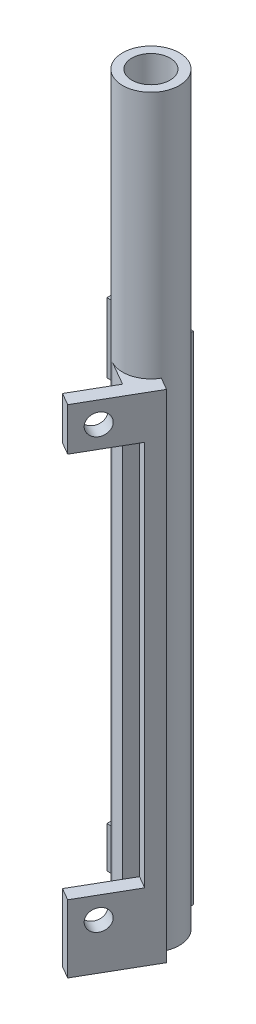
SolidWorks part; units mm, degrees
ref_plane "Front Plane" through (0, 0, 0) normal (0, 0, 1) x (1, 0, 0)
ref_plane "Top Plane" through (0, 0, 0) normal (0, 1, 0) x (1, 0, 0)
ref_plane "Right Plane" through (0, 0, 0) normal (1, 0, 0) x (0, 0, -1)
sketch "Sketch1" plane through (0, 0, 0) normal (0, 1, 0) x (1, 0, 0)
  circle A0 centre (0, 0) radius 5.08
  dimension "D1" = 10.16
extrude "Boss-Extrude1" add sketch "Sketch1" along normal blind 133.35
sketch "Sketch2" plane through (0, 0, 0) normal (0, -1, 0) x (1, 0, 0)
  circle A0 centre (0, 0) radius 3.429
  dimension "D1" = 6.858
extrude "Cut-Extrude1" cut sketch "Sketch2" against normal through all
sketch "Sketch3" plane through (0, 0, 0) normal (0, -1, 0) x (1, 0, 0)
  line L0 (0, 0) -> (0, -5.08) construction
  line L1 (0, -5.08) -> (-5.08, -5.08) construction
  line L2 (0, 0) -> (-2.54, 4.3994) construction
  line L3 (0, 0) -> (-5.08, 0) construction
  line L4 (-2.54, 4.3994) -> (1.8594, 6.9394) construction
  line L5 (8.7988, -5.08) -> (-1.4426, 12.6586) construction
  line L7 (0, -5.08) -> (-11.684, -5.08) construction
  line L8 (-1.4426, 12.6586) -> (-5.842, 10.1186)
  line L9 (-11.684, -5.08) -> (-11.684, 0)
  line L10 (-5.842, 10.1186) -> (-2.54, 4.3994)
  line L11 (-11.684, 0) -> (-5.08, 0)
  line L13 (-11.684, -5.08) -> (-11.684, -10.16)
  line L14 (-11.684, -10.16) -> (0, -10.16)
  line L15 (0, -10.16) -> (0, -5.08)
  line L17 (4.3994, 2.54) -> (8.7988, 5.08)
  line L18 (8.7988, 5.08) -> (2.9568, 15.1986)
  line L19 (2.9568, 15.1986) -> (-1.4426, 12.6586)
  arc A0 (-5.08, 0) -> (-2.54, 4.3994) centre (-0.7771, 0.4486) ccw
  circle A1 centre (0, 0) radius 3.429 construction
  circle A2 centre (0, 0) radius 5.08 construction
  arc A3 (4.3994, 2.54) -> (0, -5.08) centre (0, 0) cw
  point P9 (0, -5.08)
  dimension "D1" = 60
  dimension "D2" = 6.604
  dimension "D3" = 6.604
  dimension "D4" = 5.08
  dimension "D5" = 5.08
  dimension "D6" = 5.08
  dimension "D7" = 5.08
extrude "Boss-Extrude2" add sketch "Sketch3" against normal blind 88.9
sketch "Sketch4" plane through (0, 0, 0) normal (0, 0, 1) x (1, 0, 0)
  line L1 (-5.08, 88.9) -> (-5.08, 0) construction
  line L2 (-5.08, 88.9) -> (-11.684, 88.9) construction
  line L4 (-5.08, 0) -> (-11.684, 0) construction
  circle A0 centre (-8.89, 80.01) radius 1.905
  circle A1 centre (-8.89, 3.81) radius 1.905
  dimension "D3" = 3.81
  dimension "D5" = 3.81
  dimension "D2" = 76.2
  dimension "D1" = 8.89
  dimension "D4" = 3.81
extrude "Hole Cuts 1" cut sketch "Sketch4" against normal up to next
sketch "Sketch7" plane through (0, 0, 0) normal (0.866, 0, 0.5) x (0.5, 0, -0.866)
  line L0 (0, 0) -> (-11.684, 0) construction
  line L1 (-5.08, 88.9) -> (-5.08, 0) construction
  line L3 (-2.54, 88.9) -> (-5.842, 88.9) construction
  circle A0 centre (-8.89, 85.09) radius 1.905
  circle A1 centre (-8.89, 8.255) radius 1.905
  dimension "D2" = 3.81
  dimension "D5" = 8.255
  dimension "D1" = 3.81
  dimension "D3" = 3.81
  dimension "D4" = 76.835
extrude "Hole Cuts 2" cut sketch "Sketch7" along normal up to next
sketch "Sketch8" plane through (0, 0, 0) normal (0, -1, 0) x (1, 0, 0)
  line L0 (-5.842, 10.1186) -> (-1.8825, 12.4046)
  line L1 (2.9568, 15.1986) -> (-5.842, 10.1186) construction
  line L2 (-11.684, 0) -> (-11.684, -4.572)
  line L3 (-11.684, 0) -> (-11.684, -10.16) construction
  line L4 (-5.842, 10.1186) -> (-2.54, 4.3994)
  line L5 (-11.684, 0) -> (-5.08, 0)
  line L6 (-1.8825, 12.4046) -> (1.4195, 6.6854)
  line L7 (1.4195, 6.6854) -> (-2.54, 4.3994)
  line L8 (-11.684, -4.572) -> (-5.08, -4.572)
  line L9 (-5.08, -4.572) -> (-5.08, 0)
  dimension "D1" = 4.572
extrude "Cut-Extrude7" cut sketch "Sketch8" against normal up to next
sketch "Sketch9" plane through (0, 0, -10.16) normal (0, 0, -1) x (-1, 0, 0)
  line L1 (11.684, 88.9) -> (0, 88.9)
  line L2 (11.684, 88.9) -> (11.684, 0)
  line L3 (11.684, 0) -> (0, 0)
  line L4 (0, 88.9) -> (0, 0)
extrude "Cut-Extrude8" cut sketch "Sketch9" against normal blind 2.54
sketch "Sketch10" plane through (8.7988, 0, 5.08) normal (0.866, 0, 0.5) x (0.5, 0, -0.866)
  line L1 (-11.684, 0) -> (0, 0)
  line L2 (-11.684, 0) -> (-11.684, 88.9)
  line L3 (-11.684, 88.9) -> (0, 88.9)
  line L4 (0, 0) -> (0, 88.9)
extrude "Cut-Extrude9" cut sketch "Sketch10" against normal blind 2.54
sketch "Sketch11" plane through (0, 0, -4.572) normal (0, 0, 1) x (1, 0, 0)
  line L1 (-11.684, 88.9) -> (-5.08, 88.9)
  line L2 (-11.684, 88.9) -> (-11.684, 0)
  line L3 (-11.684, 0) -> (-5.08, 0)
  line L4 (-5.08, 88.9) -> (-5.08, 0)
extrude "Cut-Extrude10" cut sketch "Sketch11" against normal blind 0.508
sketch "Sketch13" plane through (3.9595, 0, 2.286) normal (-0.866, 0, -0.5) x (-0.5, 0, 0.866)
  line L1 (5.08, 0) -> (11.684, 0)
  line L2 (5.08, 0) -> (5.08, 88.9)
  line L3 (5.08, 88.9) -> (11.684, 88.9)
  line L4 (11.684, 0) -> (11.684, 88.9)
extrude "Cut-Extrude11" cut sketch "Sketch13" against normal blind 0.508
sketch "Sketch14" plane through (-5.842, 0, 10.1186) normal (-0.5, 0, 0.866) x (0.866, 0, 0.5)
  line L1 (7.62, 0) -> (5.08, 0)
  line L2 (7.62, 0) -> (7.62, 88.9)
  line L3 (7.62, 88.9) -> (5.08, 88.9)
  line L4 (5.08, 0) -> (5.08, 88.9)
extrude "Boss-Extrude3" add sketch "Sketch14" along normal blind 1.27
sketch "Sketch15" plane through (-11.684, 0, 0) normal (-1, 0, 0) x (0, 0, 1)
  line L1 (-5.08, 0) -> (-7.62, 0)
  line L2 (-5.08, 0) -> (-5.08, 88.9)
  line L3 (-5.08, 88.9) -> (-7.62, 88.9)
  line L4 (-7.62, 0) -> (-7.62, 88.9)
extrude "Boss-Extrude4" add sketch "Sketch15" along normal blind 1.27
sketch "Sketch20" plane through (0, 0, -5.08) normal (0, 0, 1) x (1, 0, 0)
  line L0 (-8.89, 80.01) -> (-8.89, 3.81) construction
  line L1 (-12.954, 0) -> (-12.954, 88.9) construction
  line L2 (-12.954, 76.454) -> (-2.8575, 76.454)
  line L3 (-12.954, 76.454) -> (-12.954, 7.366)
  line L4 (-12.954, 7.366) -> (-2.8575, 7.366)
  line L5 (-2.8575, 76.454) -> (-2.8575, 7.366)
  point P12 (-8.89, 41.91)
  point P13 (-12.954, 41.91)
  dimension "D1" = 69.088
  dimension "D2" = 10.0965
extrude "Cut-Extrude13" cut sketch "Sketch20" against normal blind 2.54
sketch "Sketch21" plane through (6.5991, 0, 3.81) normal (0.866, 0, 0.5) x (0.5, 0, -0.866)
  line L0 (-8.89, 85.09) -> (-8.89, 8.255) construction
  line L1 (-12.954, 0) -> (-12.954, 88.9) construction
  line L2 (-12.954, 81.2165) -> (-2.8575, 81.2165)
  line L3 (-12.954, 81.2165) -> (-12.954, 12.1285)
  line L4 (-12.954, 12.1285) -> (-2.8575, 12.1285)
  line L5 (-2.8575, 81.2165) -> (-2.8575, 12.1285)
  point P12 (-8.89, 46.6725)
  point P13 (-12.954, 46.6725)
  dimension "D1" = 69.088
  dimension "D2" = 10.0965
extrude "Cut-Extrude14" cut sketch "Sketch21" against normal blind 2.54
